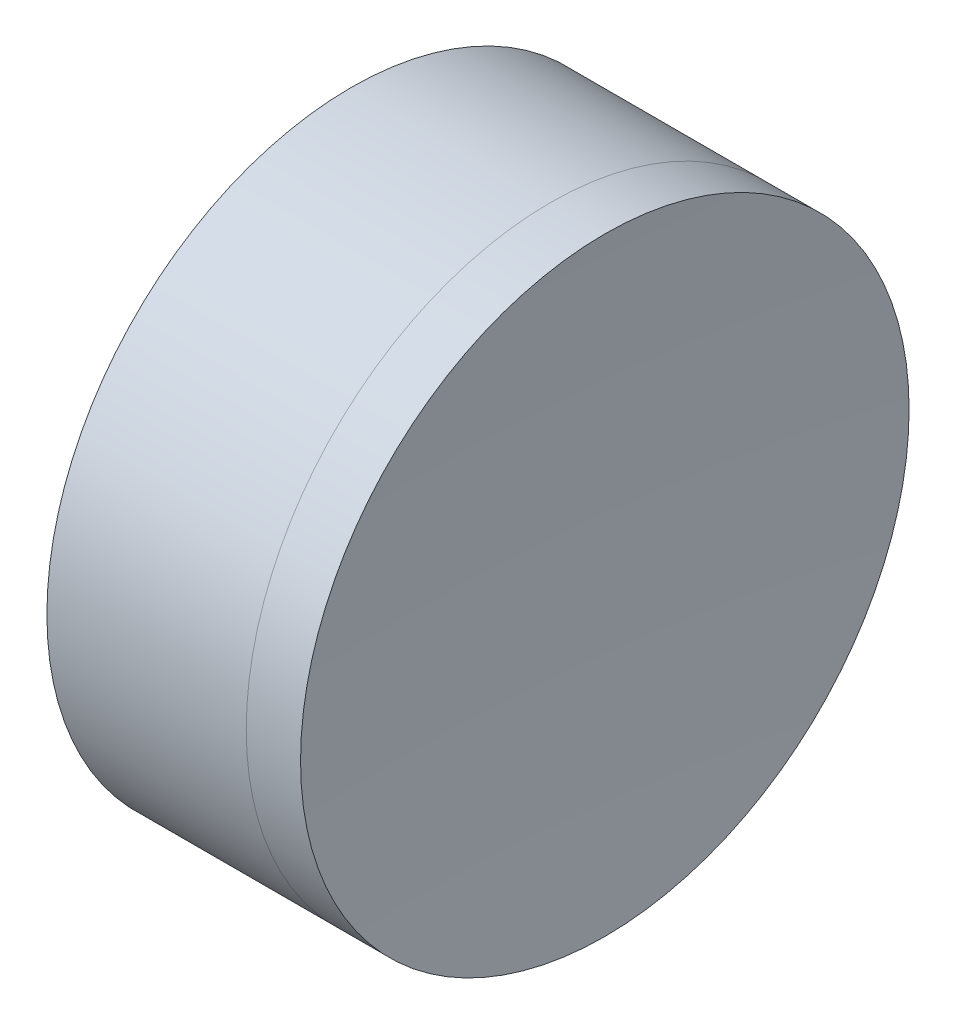
SolidWorks part; units mm, degrees
ref_plane "前视基准面" through (0, 0, 0) normal (0, 0, 1) x (1, 0, 0)
ref_plane "上视基准面" through (0, 0, 0) normal (0, 1, 0) x (1, 0, 0)
ref_plane "右视基准面" through (0, 0, 0) normal (1, 0, 0) x (0, 0, -1)
sketch "草图1" plane through (0, 0, 0) normal (0, 1, 0) x (1, 0, 0)
  line L0 (-0.8161, 0) -> (467.1828, 0) construction
  line L1 (257.1233, 12.7) -> (265.4435, 12.7)
  line L4 (257.1233, -12.7) -> (265.4435, -12.7)
  arc A0 (257.1233, -12.7) -> (257.1233, 12.7) centre (233.1834, 0) ccw
  arc A1 (265.4435, 12.7) -> (265.4435, -12.7) centre (289.3834, 0) ccw
  point P6 (260.2834, 0)
  point P8 (262.2834, 0)
  dimension "D3" = 12.7
  dimension "D4" = 2
  dimension "D1" = 27.1
  dimension "D5" = 27.1
  dimension "D2" = 12.7
revolve "旋转1" add sketch "草图1" angle 360 about L0
sketch "草图2" plane through (0, 0, 0) normal (0, 1, 0) x (1, 0, 0)
  line L2 (257.1233, 0) -> (272.9951, 0) construction
  line L3 (257.1233, -12.7) -> (257.1233, 12.7) construction
  line L6 (265.4435, 12.7) -> (267.7101, 12.7)
  line L7 (265.4435, -12.7) -> (267.7101, -12.7)
  arc A2 (265.4435, 12.7) -> (265.4435, -12.7) centre (289.3834, 0) ccw construction
  arc A3 (265.4435, 12.7) -> (265.4435, -12.7) centre (289.3834, 0) ccw
  arc A4 (267.7101, 12.7) -> (267.7101, -12.7) centre (456.4834, 0) ccw
  point P8 (262.2834, 0)
  point P9 (267.2834, 0)
  point P10 (257.1233, 0)
  point P13 (257.1233, 0)
  point P15 (257.1233, 0)
  point P16 (257.1233, 0)
  point P17 (257.1233, 0)
  point P18 (272.9951, 0)
  dimension "D1" = 5
  dimension "D2" = 189.2
revolve "旋转3" add sketch "草图2" angle 360 about L2
